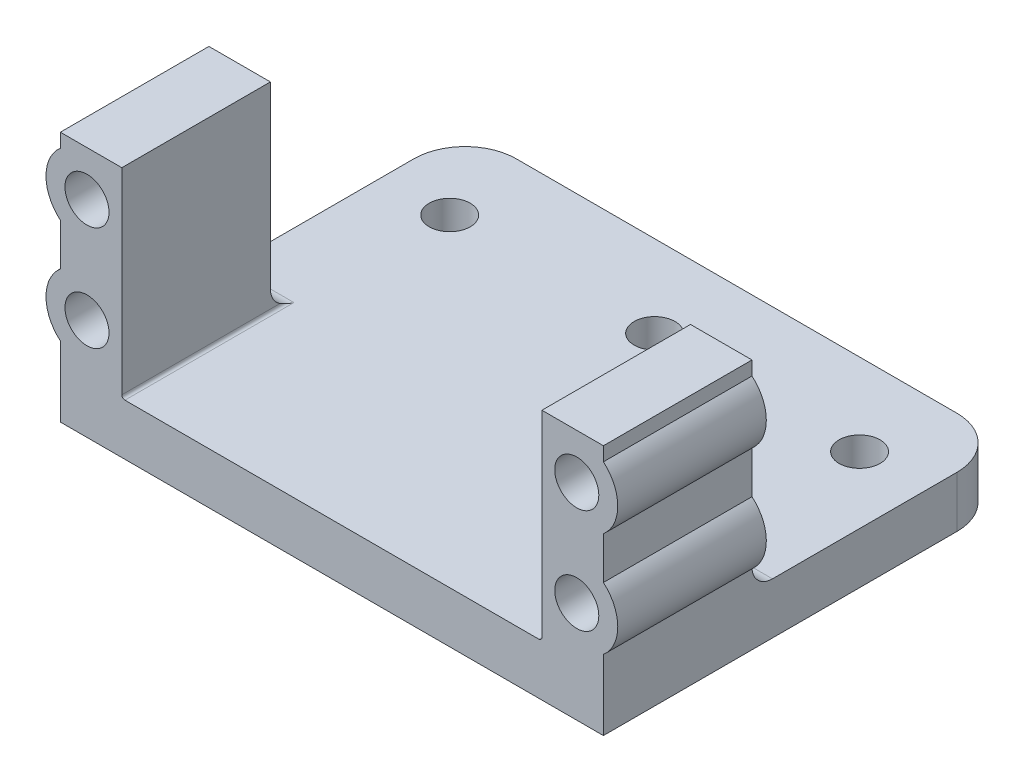
SolidWorks part; units mm, degrees
ref_plane "Front Plane" through (0, 0, 0) normal (0, 0, 1) x (1, 0, 0)
ref_plane "Top Plane" through (0, 0, 0) normal (0, 1, 0) x (1, 0, 0)
ref_plane "Right Plane" through (0, 0, 0) normal (1, 0, 0) x (0, 0, -1)
sketch "Sketch1" plane through (0, 0, 0) normal (0, 0, 1) x (1, 0, 0)
  line L1 (-20.5, 2.5) -> (20.5, 2.5)
  line L5 (26.5, -2.5) -> (26.5, 22)
  line L6 (26.5, 22) -> (20.5, 22)
  line L7 (20.5, 22) -> (20.5, 2.5)
  line L9 (-26.5, -2.5) -> (-26.5, 22)
  line L10 (-26.5, 22) -> (-20.5, 22)
  line L11 (-20.5, 22) -> (-20.5, 2.5)
  line L12 (-26.5, -2.5) -> (26.5, -2.5)
  dimension "D1" = 41
  dimension "D2" = 2.5
  dimension "D3" = 20.5
  dimension "D4" = 6
  dimension "D5" = 6
  dimension "D6" = 24.5
  dimension "D7" = 5
extrude "Boss-Extrude1" add sketch "Sketch1" along normal blind 26.5
sketch "Sketch4" plane through (0, 22, 0) normal (0, 1, 0) x (1, 0, 0)
  line L0 (-26.5, -26.5) -> (-26.5, 0) construction
  line L1 (-26.5, -12) -> (-20.5, -12)
  line L2 (-26.5, -12) -> (-26.5, 0)
  line L3 (-26.5, 0) -> (-20.5, 0)
  line L4 (-20.5, -12) -> (-20.5, 0)
  line L5 (0, 0) -> (0, -19.8022) construction
  line L6 (20.5, -12) -> (20.5, 0)
  line L7 (26.5, 0) -> (20.5, 0)
  line L8 (26.5, -12) -> (26.5, 0)
  line L9 (26.5, -12) -> (20.5, -12)
  dimension "D1" = 12
extrude "Cut-Extrude2" cut sketch "Sketch4" against normal up to surface (19.5 mm away) up to face at (0, 2.5, 13.25)
fillet "Fillet2" radius 0.3 1 edges at (20.5, 2.5, 19.25)
fillet "Fillet3" radius 0.3 1 edges at (-20.5, 2.5, 19.25)
sketch "Sketch7" plane through (0, 0, 26.5) normal (0, 0, 1) x (1, 0, 0)
  line L0 (20.5, 22) -> (20.5, 2.8) construction
  line L1 (20.5, 19.7071) -> (20.5, 15.4929)
  line L2 (20.5, 9.5071) -> (20.5, 5.2929)
  arc A0 (20.5, 5.2929) -> (20.5, 9.5071) centre (23.9, 7.4) ccw
  arc A1 (20.5, 15.4929) -> (20.5, 19.7071) centre (23.9, 17.6) ccw
  dimension "D1" = 8
  dimension "D2" = 8
extrude "Boss-Extrude3" add sketch "Sketch7" along direction (0, 0, 1) on the side against the normal up to surface (14.5 mm away)
ref_plane "Plane1" through (0, 0, 0) normal (-1, 0, 0) x (0, 0, 1)
sketch "Sketch8" plane through (0, 0, 26.5) normal (0, 0, 1) x (1, 0, 0)
  circle A1 centre (23.9, 17.6) radius 2.15
  circle A2 centre (23.9, 7.4) radius 2.15
  dimension "D1" = 4.3
  dimension "D2" = 4.3
extrude "Cut-Extrude4" cut sketch "Sketch8" against normal up to surface (14.5 mm away) up to face at (24.7847, 11.3042, 12)
mirror "Mirror3" about plane through (0, 0, 0) normal (-1, 0, 0) of "Boss-Extrude3", "Cut-Extrude4"
fillet "Fillet4" radius 2 2 edges at (-23.35, 2.5, 12) (23.35, 2.5, 12)
sketch "Sketch9" plane through (0, 0, 0) normal (0, 0, -1) x (-1, 0, 0)
  line L4 (26.5, -2.5) -> (26.5, 2.5)
  line L5 (26.5, 2.5) -> (-26.5, 2.5)
  line L6 (-26.5, 2.5) -> (-26.5, -2.5)
  line L7 (-26.5, -2.5) -> (26.5, -2.5)
  line L8 (26.5, -2.5) -> (26.5, 2.5)
  line L9 (26.5, 2.5) -> (-26.5, 2.5)
  line L10 (-26.5, 2.5) -> (-26.5, -2.5)
  line L11 (-26.5, -2.5) -> (26.5, -2.5)
  dimension "D1" = 0
extrude "Boss-Extrude4" add sketch "Sketch9" along normal blind 13
sketch "Sketch10" plane through (0, 2.5, 0) normal (0, 1, 0) x (1, 0, 0)
  line L0 (0, 0) -> (-11.2026, 0) construction
  line L1 (0, 0) -> (0, -7.0349) construction
  circle A0 centre (20, 5) radius 2
  circle A1 centre (0, 5) radius 2
  circle A2 centre (-20, 5) radius 2
  dimension "D1" = 4
  dimension "D2" = 4
  dimension "D3" = 4
  dimension "D4" = 5
  dimension "D5" = 20
  dimension "D6" = 20
extrude "Cut-Extrude5" cut sketch "Sketch10" against normal blind 10
fillet "Fillet9" radius 5 2 edges at (-26.5, 0, -13) (26.5, 0, -13)
sketch "Sketch11" plane through (0, 0, 26.5) normal (0, 0, 1) x (1, 0, 0)
  line L0 (26.5, -2.5) -> (26.5, 4.3603) construction
  line L1 (-26.5, -2.5) -> (26.5, -2.5)
  line L2 (-26.5, -2.5) -> (-26.5, 2.5)
  line L3 (-26.5, 2.5) -> (26.5, 2.5)
  line L4 (26.5, -2.5) -> (26.5, 2.5)
  line L5 (20.2, 2.5) -> (-20.2, 2.5) construction
extrude "Boss-Extrude5" add sketch "Sketch11" along normal blind 6.5
fillet "Fillet11" radius 5 2 edges at (-26.5, 0, 33) (26.5, 0, 33)
sketch "Sketch12" plane through (0, 2.5, 0) normal (0, 1, 0) x (1, 0, 0)
  line L0 (-20.5, -26.5) -> (-26.5, -26.5) construction
  line L1 (-29.2677, -26.5) -> (28.0753, -26.5)
  line L2 (-29.2677, -26.5) -> (-29.2677, -33.6768)
  line L3 (-29.2677, -33.6768) -> (28.0753, -33.6768)
  line L4 (28.0753, -26.5) -> (28.0753, -33.6768)
extrude "Cut-Extrude6" cut sketch "Sketch12" against normal blind 5
